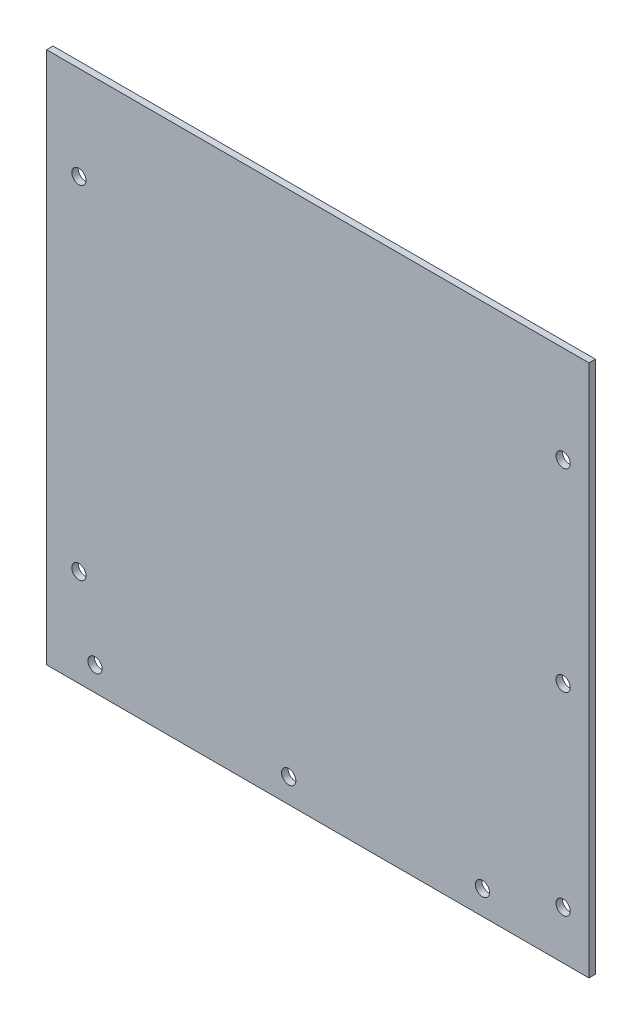
SolidWorks part; units mm, degrees
ref_plane "正面" through (0, 0, 0) normal (0, 0, 1) x (1, 0, 0)
ref_plane "平面" through (0, 0, 0) normal (0, 1, 0) x (1, 0, 0)
ref_plane "右側面" through (0, 0, 0) normal (1, 0, 0) x (0, 0, -1)
sketch "ｽｹｯﾁ1" plane through (0, 0, 0) normal (0, 0, 1) x (1, 0, 0)
  line L1 (-84, 83.5) -> (84, 83.5)
  line L2 (-84, 83.5) -> (-84, -83.5)
  line L3 (-84, -83.5) -> (84, -83.5)
  line L4 (84, 83.5) -> (84, -83.5)
  line L5 (-84, 83.5) -> (84, -83.5) construction
  line L6 (-84, -83.5) -> (84, 83.5) construction
  point P0 (0, 0)
  dimension "D1" = 167
  dimension "D2" = 168
extrude "ﾎﾞｽ - 押し出し1" add sketch "ｽｹｯﾁ1" along normal blind 2
sketch "ｽｹｯﾁ2" plane through (0, 0, 2) normal (0, 0, 1) x (1, 0, 0)
  line L0 (84, -83.5) -> (76, -83.5)
  line L1 (-84, -83.5) -> (84, -83.5) construction
  line L2 (76, -83.5) -> (76, -68.5)
  line L3 (76, -68.5) -> (76, -20.6241)
  line L4 (76, -83.5) -> (76, -8.5)
  line L5 (76, -83.5) -> (76, 51.5)
  circle A0 centre (76, -68.5) radius 2.2
  circle A1 centre (76, -8.5) radius 2.2
  circle A2 centre (76, 51.5) radius 2.2
  dimension "D5" = 4.4
  dimension "D6" = 4.4
  dimension "D7" = 4.4
  dimension "D1" = 8
  dimension "D2" = 15
  dimension "D3" = 75
  dimension "D4" = 135
extrude "ｶｯﾄ - 押し出し1" cut sketch "ｽｹｯﾁ2" against normal blind 2
sketch "ｽｹｯﾁ3" plane through (0, 83.5, 0) normal (0, 1, 0) x (1, 0, 0)
  line L1 (-84, -2) -> (84, -2)
  line L2 (-84, -2) -> (-84, 0)
  line L3 (-84, 0) -> (84, 0)
  line L4 (84, -2) -> (84, 0)
extrude "ｶｯﾄ - 押し出し2" cut sketch "ｽｹｯﾁ3" against normal blind 2
sketch "ｽｹｯﾁ4" plane through (0, 0, 2) normal (0, 0, 1) x (1, 0, 0)
  line L0 (-84, -83.5) -> (-84, -76)
  line L1 (-84, 81.5) -> (-84, -83.5) construction
  line L2 (-84, -76) -> (-69, -76)
  line L3 (-84, -76) -> (-9, -76)
  line L4 (-84, -76) -> (51, -76)
  circle A0 centre (-69, -76) radius 2.2
  circle A1 centre (-9, -76) radius 2.2
  circle A2 centre (51, -76) radius 2.2
  dimension "D5" = 4.4
  dimension "D6" = 4.4
  dimension "D7" = 4.4
  dimension "D1" = 7.5
  dimension "D2" = 15
  dimension "D3" = 75
  dimension "D4" = 135
extrude "ｶｯﾄ - 押し出し3" cut sketch "ｽｹｯﾁ4" against normal blind 2 contours L3 A1 L4 | L4 A1 L3 | L4 A0 L3 | L3 A0 L4 | A2
sketch "ｽｹｯﾁ6" plane through (0, 0, 0) normal (0, 0, -1) x (-1, 0, 0)
  line L0 (84, -83.5) -> (74, -83.5)
  line L1 (84, -83.5) -> (-84, -83.5) construction
  line L2 (74, -83.5) -> (74, 52.5)
  circle A0 centre (74, 52.5) radius 2.2
  dimension "D2" = 4.4
  dimension "D1" = 10
  dimension "D3" = 136
extrude "ｶｯﾄ - 押し出し5" cut sketch "ｽｹｯﾁ6" against normal blind 10
sketch "ｽｹｯﾁ7" plane through (0, 0, 0) normal (0, 0, -1) x (-1, 0, 0)
  line L0 (69, -76) -> (74, -76)
  line L1 (74, -76) -> (74, -53.5)
  circle A0 centre (74, -53.5) radius 2.2
  dimension "D3" = 4.4
  dimension "D1" = 5
  dimension "D2" = 22.5
extrude "ｶｯﾄ - 押し出し6" cut sketch "ｽｹｯﾁ7" against normal blind 10
